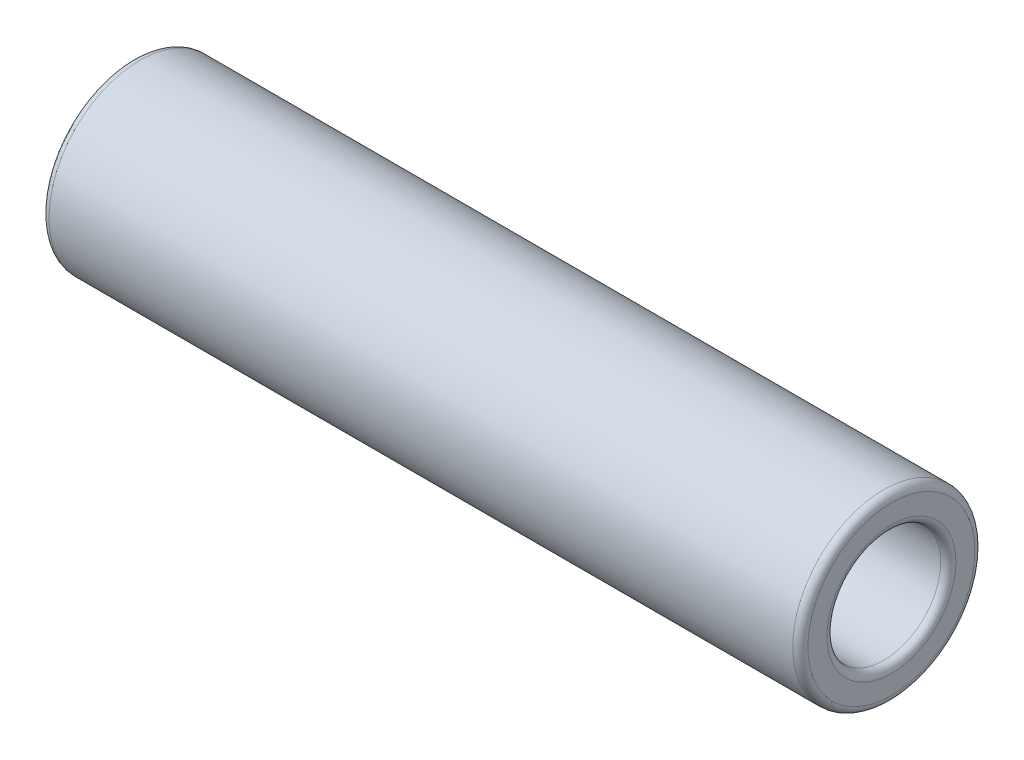
SolidWorks part; units mm, degrees
material "Plain Carbon Steel"
ref_plane "Front Plane" through (0, 0, 0) normal (0, 0, 1) x (1, 0, 0)
ref_plane "Top Plane" through (0, 0, 0) normal (0, 1, 0) x (1, 0, 0)
ref_plane "Right Plane" through (0, 0, 0) normal (1, 0, 0) x (0, 0, -1)
sketch "Sketch1" plane through (0, 0, 0) normal (1, 0, 0) x (0, 0, -1)
  circle A0 centre (0, 0) radius 6
  circle A1 centre (0, 0) radius 3.75
  dimension "D1" = 12
  dimension "D2" = 7.5
extrude "Boss-Extrude1" add sketch "Sketch1" along normal blind 50
fillet "Fillet1" radius 0.5 4 edges at (50, 0, -3.75) (50, 0, -6) (0, 0, -3.75) (0, 0, -6)
